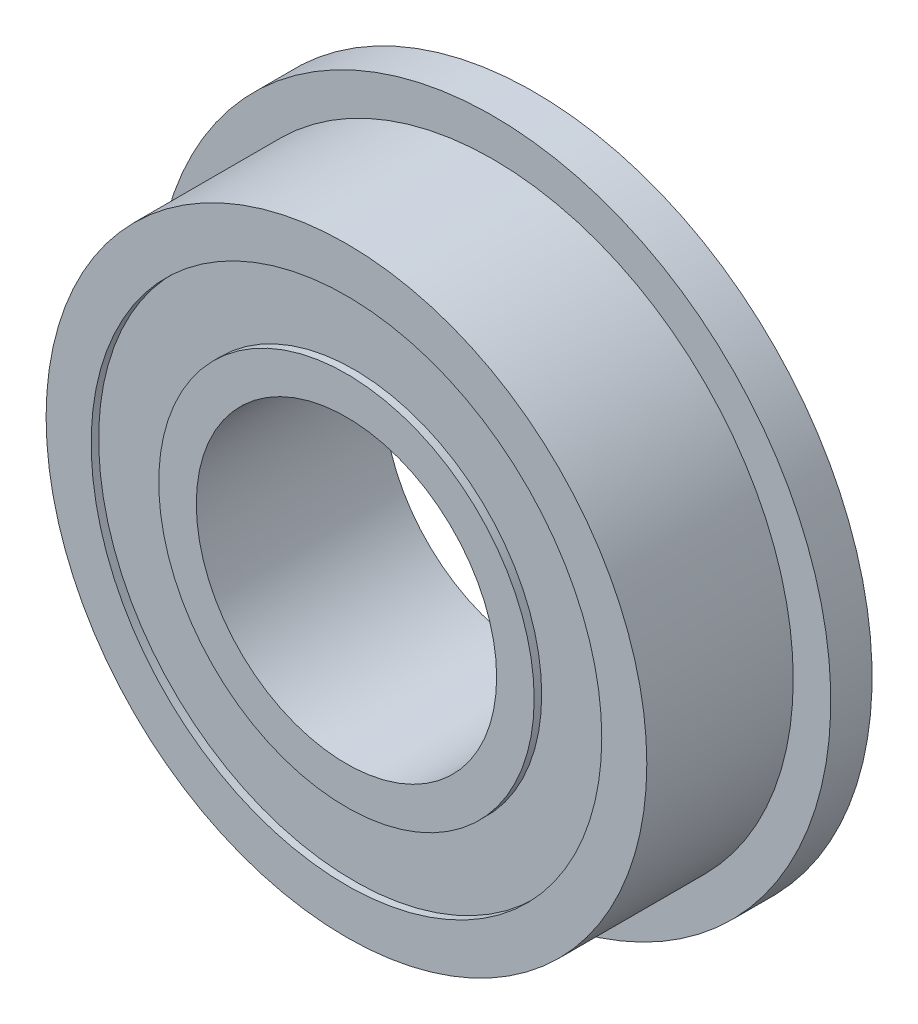
SolidWorks part; units mm, degrees
material "鉻不鏽鋼"
ref_plane "前基準面" through (0, 0, 0) normal (0, 0, 1) x (1, 0, 0)
ref_plane "上基準面" through (0, 0, 0) normal (0, 1, 0) x (1, 0, 0)
ref_plane "右基準面" through (0, 0, 0) normal (1, 0, 0) x (0, 0, -1)
sketch "草圖1" plane through (0, 0, 0) normal (0, 0, 1) x (1, 0, 0)
  circle A0 centre (0, 0) radius 8
  dimension "D1" = 16
extrude "填料-伸長1" add sketch "草圖1" along normal mid plane 5
sketch "草圖4" plane through (0, 0, -2.5) normal (0, 0, -1) x (-1, 0, 0)
  circle A0 centre (0, 0) radius 9
  dimension "D1" = 18
extrude "填料-伸長2" add sketch "草圖4" against normal blind 1.1
sketch "草圖2" plane through (0, 0, 2.5) normal (0, 0, 1) x (1, 0, 0)
  circle A0 centre (0, 0) radius 4
  dimension "D1" = 8
extrude "除料-伸長1" cut sketch "草圖2" against normal through all
sketch "草圖3" plane through (0, 0, 2.5) normal (0, 0, 1) x (1, 0, 0)
  circle A0 centre (0, 0) radius 6.8
  circle A1 centre (0, 0) radius 5
  dimension "D1" = 10
  dimension "D2" = 13.6
extrude "除料-伸長2" cut sketch "草圖3" against normal blind 0.2
mirror "鏡射1" about plane through (0, 0, 0) normal (0, 0, 1) of "除料-伸長2"
